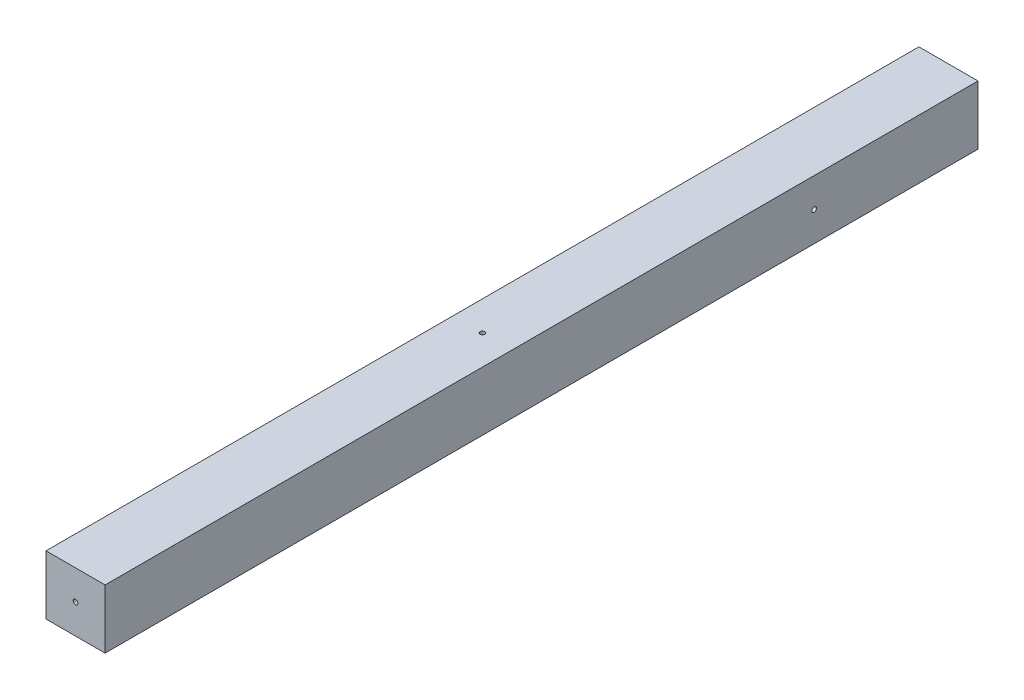
SolidWorks part; units mm, degrees
material "Pin"
ref_plane "Plan de face" through (0, 0, 0) normal (0, 0, 1) x (1, 0, 0)
ref_plane "Plan de dessus" through (0, 0, 0) normal (0, 1, 0) x (1, 0, 0)
ref_plane "Plan de droite" through (0, 0, 0) normal (1, 0, 0) x (0, 0, -1)
sketch "Esquisse1" plane through (0, 0, 0) normal (0, 0, 1) x (1, 0, 0)
  line L1 (22, 22) -> (-22, 22)
  line L2 (22, 22) -> (22, -22)
  line L3 (22, -22) -> (-22, -22)
  line L4 (-22, 22) -> (-22, -22)
  line L5 (22, 22) -> (-22, -22) construction
  line L6 (22, -22) -> (-22, 22) construction
  point P0 (0, 0)
extrude "Boss.-Extru.1" add sketch "Esquisse1" along normal blind 650
sketch "Esquisse2" plane through (0, 0, 650) normal (0, 0, -1) x (-1, 0, 0)
  circle A0 centre (0, 0) radius 1.75
  dimension "D1" = 3.5
extrude "Enlèv. mat.-Extru.1" cut sketch "Esquisse2" along normal blind 60
sketch "Esquisse3" plane through (-22, 0, 0) normal (1, 0, 0) x (0, 1, 0)
  line L0 (-22, 650) -> (-22, 0) construction
  line L2 (22, 0) -> (-22, 0) construction
  circle A0 centre (0, 122) radius 1.75
  dimension "D1" = 3.5
  dimension "D2" = 22
  dimension "D3" = 122
extrude "Enlèv. mat.-Extru.2" cut sketch "Esquisse3" along normal up to surface (44 mm away) up to face at (22, 0, 325)
sketch "Esquisse4" plane through (0, -22, 0) normal (0, -1, 0) x (1, 0, 0)
  line L1 (-22, 0) -> (22, 0) construction
  circle A0 centre (0, 347) radius 1.75
  dimension "D1" = 3.5
  dimension "D2" = 347
extrude "Enlèv. mat.-Extru.3" cut sketch "Esquisse4" against normal blind 60
